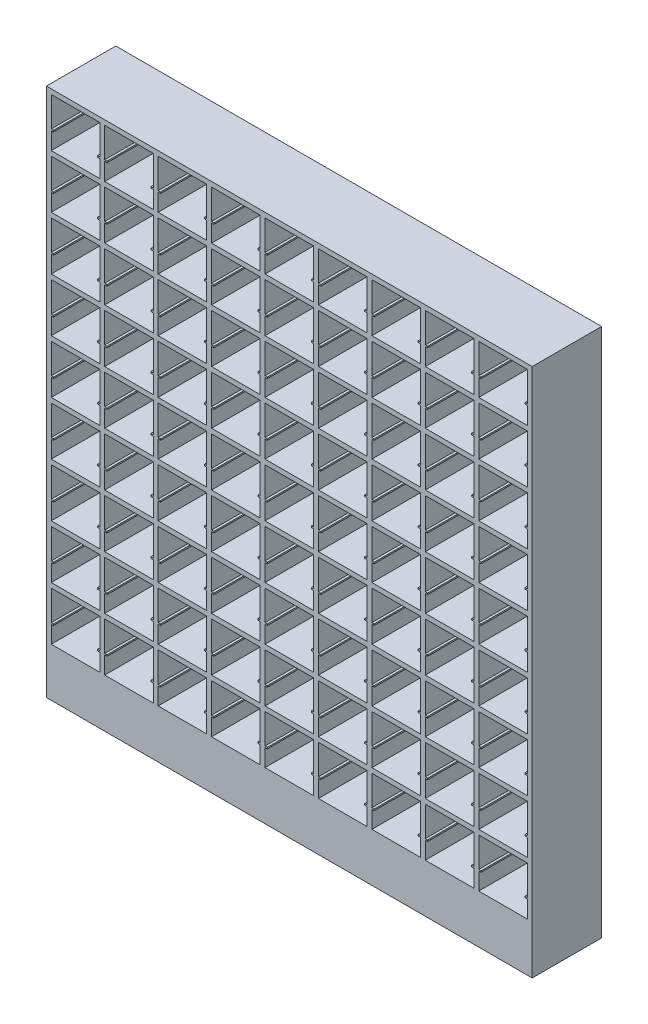
SolidWorks part; units mm, degrees
ref_plane "Alzado" through (0, 0, 0) normal (0, 0, 1) x (1, 0, 0)
ref_plane "Planta" through (0, 0, 0) normal (0, 1, 0) x (1, 0, 0)
ref_plane "Vista lateral" through (0, 0, 0) normal (1, 0, 0) x (0, 0, -1)
sketch "Croquis1" plane through (0, 0, 0) normal (0, 0, 1) x (1, 0, 0)
  line L11 (-1365, 1490) -> (-1365, 1365)
  line L330 (1750, -1750) -> (1750, 1750)
  line L331 (1750, 1750) -> (-1750, 1750)
  line L332 (-1750, -1750) -> (-1750, 1750)
  line L989 (1750, -1750) -> (-1750, 1750) construction
  line L990 (1750, 1750) -> (-1750, -1750) construction
  line L991 (-1715, 1715) -> (-1365, 1715)
  line L992 (-1715, 1715) -> (-1715, 1500)
  line L993 (-1715, 1365) -> (-1365, 1365)
  line L994 (-1365, 1715) -> (-1365, 1500)
  line L995 (-1715, 1490) -> (-1698.3333, 1490)
  line L996 (-1715, 1500) -> (-1698.3333, 1500)
  line L997 (-1698.3333, 1490) -> (-1698.3333, 1500)
  line L998 (-1365, 1490) -> (-1381.6667, 1490)
  line L1000 (-1365, 1500) -> (-1381.6667, 1500)
  line L1001 (-1381.6667, 1490) -> (-1381.6667, 1500)
  line L1002 (-1715, 1490) -> (-1715, 1365)
  line L1003 (-1330, 1715) -> (-980, 1715)
  line L1005 (-980, 1715) -> (-980, 1500)
  line L1006 (-980, 1500) -> (-996.6667, 1500)
  line L1007 (-996.6667, 1490) -> (-996.6667, 1500)
  line L1008 (-980, 1490) -> (-996.6667, 1490)
  line L1009 (-980, 1490) -> (-980, 1365)
  line L1010 (-1330, 1365) -> (-980, 1365)
  line L1011 (-1330, 1490) -> (-1330, 1365)
  line L1012 (-1330, 1490) -> (-1313.3333, 1490)
  line L1013 (-1313.3333, 1490) -> (-1313.3333, 1500)
  line L1014 (-1330, 1500) -> (-1313.3333, 1500)
  line L1015 (-1330, 1715) -> (-1330, 1500)
  line L1016 (-945, 1715) -> (-595, 1715)
  line L1017 (-595, 1715) -> (-595, 1500)
  line L1018 (-595, 1500) -> (-611.6667, 1500)
  line L1019 (-611.6667, 1490) -> (-611.6667, 1500)
  line L1020 (-595, 1490) -> (-611.6667, 1490)
  line L1021 (-595, 1490) -> (-595, 1365)
  line L1022 (-945, 1365) -> (-595, 1365)
  line L1023 (-945, 1490) -> (-945, 1365)
  line L1024 (-945, 1490) -> (-928.3333, 1490)
  line L1025 (-928.3333, 1490) -> (-928.3333, 1500)
  line L1026 (-945, 1500) -> (-928.3333, 1500)
  line L1027 (-945, 1715) -> (-945, 1500)
  line L1028 (-560, 1715) -> (-210, 1715)
  line L1029 (-210, 1715) -> (-210, 1500)
  line L1030 (-210, 1500) -> (-226.6667, 1500)
  line L1031 (-226.6667, 1490) -> (-226.6667, 1500)
  line L1032 (-210, 1490) -> (-226.6667, 1490)
  line L1033 (-210, 1490) -> (-210, 1365)
  line L1034 (-560, 1365) -> (-210, 1365)
  line L1035 (-560, 1490) -> (-560, 1365)
  line L1036 (-560, 1490) -> (-543.3333, 1490)
  line L1037 (-543.3333, 1490) -> (-543.3333, 1500)
  line L1038 (-560, 1500) -> (-543.3333, 1500)
  line L1039 (-560, 1715) -> (-560, 1500)
  line L1040 (-175, 1715) -> (175, 1715)
  line L1041 (175, 1715) -> (175, 1500)
  line L1042 (175, 1500) -> (158.3333, 1500)
  line L1043 (158.3333, 1490) -> (158.3333, 1500)
  line L1044 (175, 1490) -> (158.3333, 1490)
  line L1045 (175, 1490) -> (175, 1365)
  line L1046 (-175, 1365) -> (175, 1365)
  line L1047 (-175, 1490) -> (-175, 1365)
  line L1048 (-175, 1490) -> (-158.3333, 1490)
  line L1049 (-158.3333, 1490) -> (-158.3333, 1500)
  line L1050 (-175, 1500) -> (-158.3333, 1500)
  line L1051 (-175, 1715) -> (-175, 1500)
  line L1052 (210, 1715) -> (560, 1715)
  line L1053 (560, 1715) -> (560, 1500)
  line L1054 (560, 1500) -> (543.3333, 1500)
  line L1055 (543.3333, 1490) -> (543.3333, 1500)
  line L1056 (560, 1490) -> (543.3333, 1490)
  line L1057 (560, 1490) -> (560, 1365)
  line L1058 (210, 1365) -> (560, 1365)
  line L1059 (210, 1490) -> (210, 1365)
  line L1060 (210, 1490) -> (226.6667, 1490)
  line L1061 (226.6667, 1490) -> (226.6667, 1500)
  line L1062 (210, 1500) -> (226.6667, 1500)
  line L1063 (210, 1715) -> (210, 1500)
  line L1064 (595, 1715) -> (945, 1715)
  line L1065 (945, 1715) -> (945, 1500)
  line L1066 (945, 1500) -> (928.3333, 1500)
  line L1067 (928.3333, 1490) -> (928.3333, 1500)
  line L1068 (945, 1490) -> (928.3333, 1490)
  line L1069 (945, 1490) -> (945, 1365)
  line L1070 (595, 1365) -> (945, 1365)
  line L1071 (595, 1490) -> (595, 1365)
  line L1072 (595, 1490) -> (611.6667, 1490)
  line L1073 (611.6667, 1490) -> (611.6667, 1500)
  line L1074 (595, 1500) -> (611.6667, 1500)
  line L1075 (595, 1715) -> (595, 1500)
  line L1076 (980, 1715) -> (1330, 1715)
  line L1077 (1330, 1715) -> (1330, 1500)
  line L1078 (1330, 1500) -> (1313.3333, 1500)
  line L1079 (1313.3333, 1490) -> (1313.3333, 1500)
  line L1080 (1330, 1490) -> (1313.3333, 1490)
  line L1081 (1330, 1490) -> (1330, 1365)
  line L1082 (980, 1365) -> (1330, 1365)
  line L1083 (980, 1490) -> (980, 1365)
  line L1084 (980, 1490) -> (996.6667, 1490)
  line L1085 (996.6667, 1490) -> (996.6667, 1500)
  line L1086 (980, 1500) -> (996.6667, 1500)
  line L1087 (980, 1715) -> (980, 1500)
  line L1088 (1365, 1715) -> (1715, 1715)
  line L1089 (1715, 1715) -> (1715, 1500)
  line L1090 (1715, 1500) -> (1698.3333, 1500)
  line L1091 (1698.3333, 1490) -> (1698.3333, 1500)
  line L1092 (1715, 1490) -> (1698.3333, 1490)
  line L1093 (1715, 1490) -> (1715, 1365)
  line L1094 (1365, 1365) -> (1715, 1365)
  line L1095 (1365, 1490) -> (1365, 1365)
  line L1096 (1365, 1490) -> (1381.6667, 1490)
  line L1097 (1381.6667, 1490) -> (1381.6667, 1500)
  line L1098 (1365, 1500) -> (1381.6667, 1500)
  line L1099 (1365, 1715) -> (1365, 1500)
  line L1100 (-1330, 1330) -> (-980, 1330)
  line L1101 (-980, 1330) -> (-980, 1115)
  line L1102 (-980, 1115) -> (-996.6667, 1115)
  line L1103 (-996.6667, 1105) -> (-996.6667, 1115)
  line L1104 (-980, 1105) -> (-996.6667, 1105)
  line L1105 (-980, 1105) -> (-980, 980)
  line L1106 (-1330, 980) -> (-980, 980)
  line L1107 (-1330, 1105) -> (-1330, 980)
  line L1108 (-1330, 1105) -> (-1313.3333, 1105)
  line L1109 (-1313.3333, 1105) -> (-1313.3333, 1115)
  line L1110 (-1330, 1115) -> (-1313.3333, 1115)
  line L1111 (-1330, 1330) -> (-1330, 1115)
  line L1112 (-945, 1330) -> (-595, 1330)
  line L1113 (-595, 1330) -> (-595, 1115)
  line L1114 (-595, 1115) -> (-611.6667, 1115)
  line L1115 (-611.6667, 1105) -> (-611.6667, 1115)
  line L1116 (-595, 1105) -> (-611.6667, 1105)
  line L1117 (-595, 1105) -> (-595, 980)
  line L1118 (-945, 980) -> (-595, 980)
  line L1119 (-945, 1105) -> (-945, 980)
  line L1120 (-945, 1105) -> (-928.3333, 1105)
  line L1121 (-928.3333, 1105) -> (-928.3333, 1115)
  line L1122 (-945, 1115) -> (-928.3333, 1115)
  line L1123 (-945, 1330) -> (-945, 1115)
  line L1124 (-560, 1330) -> (-210, 1330)
  line L1125 (-210, 1330) -> (-210, 1115)
  line L1126 (-210, 1115) -> (-226.6667, 1115)
  line L1127 (-226.6667, 1105) -> (-226.6667, 1115)
  line L1128 (-210, 1105) -> (-226.6667, 1105)
  line L1129 (-210, 1105) -> (-210, 980)
  line L1130 (-560, 980) -> (-210, 980)
  line L1131 (-560, 1105) -> (-560, 980)
  line L1132 (-560, 1105) -> (-543.3333, 1105)
  line L1133 (-543.3333, 1105) -> (-543.3333, 1115)
  line L1134 (-560, 1115) -> (-543.3333, 1115)
  line L1135 (-560, 1330) -> (-560, 1115)
  line L1136 (-175, 1330) -> (175, 1330)
  line L1137 (175, 1330) -> (175, 1115)
  line L1138 (175, 1115) -> (158.3333, 1115)
  line L1139 (158.3333, 1105) -> (158.3333, 1115)
  line L1140 (175, 1105) -> (158.3333, 1105)
  line L1141 (175, 1105) -> (175, 980)
  line L1142 (-175, 980) -> (175, 980)
  line L1143 (-175, 1105) -> (-175, 980)
  line L1144 (-175, 1105) -> (-158.3333, 1105)
  line L1145 (-158.3333, 1105) -> (-158.3333, 1115)
  line L1146 (-175, 1115) -> (-158.3333, 1115)
  line L1147 (-175, 1330) -> (-175, 1115)
  line L1148 (210, 1330) -> (560, 1330)
  line L1149 (560, 1330) -> (560, 1115)
  line L1150 (560, 1115) -> (543.3333, 1115)
  line L1151 (543.3333, 1105) -> (543.3333, 1115)
  line L1152 (560, 1105) -> (543.3333, 1105)
  line L1153 (560, 1105) -> (560, 980)
  line L1154 (210, 980) -> (560, 980)
  line L1155 (210, 1105) -> (210, 980)
  line L1156 (210, 1105) -> (226.6667, 1105)
  line L1157 (226.6667, 1105) -> (226.6667, 1115)
  line L1158 (210, 1115) -> (226.6667, 1115)
  line L1159 (210, 1330) -> (210, 1115)
  line L1160 (595, 1330) -> (945, 1330)
  line L1161 (945, 1330) -> (945, 1115)
  line L1162 (945, 1115) -> (928.3333, 1115)
  line L1163 (928.3333, 1105) -> (928.3333, 1115)
  line L1164 (945, 1105) -> (928.3333, 1105)
  line L1165 (945, 1105) -> (945, 980)
  line L1166 (595, 980) -> (945, 980)
  line L1167 (595, 1105) -> (595, 980)
  line L1168 (595, 1105) -> (611.6667, 1105)
  line L1169 (611.6667, 1105) -> (611.6667, 1115)
  line L1170 (595, 1115) -> (611.6667, 1115)
  line L1171 (595, 1330) -> (595, 1115)
  line L1172 (980, 1330) -> (1330, 1330)
  line L1173 (1330, 1330) -> (1330, 1115)
  line L1174 (1330, 1115) -> (1313.3333, 1115)
  line L1175 (1313.3333, 1105) -> (1313.3333, 1115)
  line L1176 (1330, 1105) -> (1313.3333, 1105)
  line L1177 (1330, 1105) -> (1330, 980)
  line L1178 (980, 980) -> (1330, 980)
  line L1179 (980, 1105) -> (980, 980)
  line L1180 (980, 1105) -> (996.6667, 1105)
  line L1181 (996.6667, 1105) -> (996.6667, 1115)
  line L1182 (980, 1115) -> (996.6667, 1115)
  line L1183 (980, 1330) -> (980, 1115)
  line L1184 (1365, 1330) -> (1715, 1330)
  line L1185 (1715, 1330) -> (1715, 1115)
  line L1186 (1715, 1115) -> (1698.3333, 1115)
  line L1187 (1698.3333, 1105) -> (1698.3333, 1115)
  line L1188 (1715, 1105) -> (1698.3333, 1105)
  line L1189 (1715, 1105) -> (1715, 980)
  line L1190 (1365, 980) -> (1715, 980)
  line L1191 (1365, 1105) -> (1365, 980)
  line L1192 (1365, 1105) -> (1381.6667, 1105)
  line L1193 (1381.6667, 1105) -> (1381.6667, 1115)
  line L1194 (1365, 1115) -> (1381.6667, 1115)
  line L1195 (1365, 1330) -> (1365, 1115)
  line L1196 (-1330, 945) -> (-980, 945)
  line L1197 (-980, 945) -> (-980, 730)
  line L1198 (-980, 730) -> (-996.6667, 730)
  line L1199 (-996.6667, 720) -> (-996.6667, 730)
  line L1200 (-980, 720) -> (-996.6667, 720)
  line L1201 (-980, 720) -> (-980, 595)
  line L1202 (-1330, 595) -> (-980, 595)
  line L1203 (-1330, 720) -> (-1330, 595)
  line L1204 (-1330, 720) -> (-1313.3333, 720)
  line L1205 (-1313.3333, 720) -> (-1313.3333, 730)
  line L1206 (-1330, 730) -> (-1313.3333, 730)
  line L1207 (-1330, 945) -> (-1330, 730)
  line L1208 (-945, 945) -> (-595, 945)
  line L1209 (-595, 945) -> (-595, 730)
  line L1210 (-595, 730) -> (-611.6667, 730)
  line L1211 (-611.6667, 720) -> (-611.6667, 730)
  line L1212 (-595, 720) -> (-611.6667, 720)
  line L1213 (-595, 720) -> (-595, 595)
  line L1214 (-945, 595) -> (-595, 595)
  line L1215 (-945, 720) -> (-945, 595)
  line L1216 (-945, 720) -> (-928.3333, 720)
  line L1217 (-928.3333, 720) -> (-928.3333, 730)
  line L1218 (-945, 730) -> (-928.3333, 730)
  line L1219 (-945, 945) -> (-945, 730)
  line L1220 (-560, 945) -> (-210, 945)
  line L1221 (-210, 945) -> (-210, 730)
  line L1222 (-210, 730) -> (-226.6667, 730)
  line L1223 (-226.6667, 720) -> (-226.6667, 730)
  line L1224 (-210, 720) -> (-226.6667, 720)
  line L1225 (-210, 720) -> (-210, 595)
  line L1226 (-560, 595) -> (-210, 595)
  line L1227 (-560, 720) -> (-560, 595)
  line L1228 (-560, 720) -> (-543.3333, 720)
  line L1229 (-543.3333, 720) -> (-543.3333, 730)
  line L1230 (-560, 730) -> (-543.3333, 730)
  line L1231 (-560, 945) -> (-560, 730)
  line L1232 (-175, 945) -> (175, 945)
  line L1233 (175, 945) -> (175, 730)
  line L1234 (175, 730) -> (158.3333, 730)
  line L1235 (158.3333, 720) -> (158.3333, 730)
  line L1236 (175, 720) -> (158.3333, 720)
  line L1237 (175, 720) -> (175, 595)
  line L1238 (-175, 595) -> (175, 595)
  line L1239 (-175, 720) -> (-175, 595)
  line L1240 (-175, 720) -> (-158.3333, 720)
  line L1241 (-158.3333, 720) -> (-158.3333, 730)
  line L1242 (-175, 730) -> (-158.3333, 730)
  line L1244 (-175, 945) -> (-175, 730)
  line L1245 (210, 945) -> (560, 945)
  line L1246 (560, 945) -> (560, 730)
  line L1247 (560, 730) -> (543.3333, 730)
  line L1248 (543.3333, 720) -> (543.3333, 730)
  line L1249 (560, 720) -> (543.3333, 720)
  line L1250 (560, 720) -> (560, 595)
  line L1251 (210, 595) -> (560, 595)
  line L1252 (210, 720) -> (210, 595)
  line L1253 (210, 720) -> (226.6667, 720)
  line L1254 (226.6667, 720) -> (226.6667, 730)
  line L1255 (210, 730) -> (226.6667, 730)
  line L1256 (210, 945) -> (210, 730)
  line L1257 (595, 945) -> (945, 945)
  line L1258 (945, 945) -> (945, 730)
  line L1259 (945, 730) -> (928.3333, 730)
  line L1260 (928.3333, 720) -> (928.3333, 730)
  line L1261 (945, 720) -> (928.3333, 720)
  line L1262 (945, 720) -> (945, 595)
  line L1263 (595, 595) -> (945, 595)
  line L1264 (595, 720) -> (595, 595)
  line L1265 (595, 720) -> (611.6667, 720)
  line L1266 (611.6667, 720) -> (611.6667, 730)
  line L1267 (595, 730) -> (611.6667, 730)
  line L1268 (595, 945) -> (595, 730)
  line L1269 (980, 945) -> (1330, 945)
  line L1270 (1330, 945) -> (1330, 730)
  line L1271 (1330, 730) -> (1313.3333, 730)
  line L1272 (1313.3333, 720) -> (1313.3333, 730)
  line L1273 (1330, 720) -> (1313.3333, 720)
  line L1274 (1330, 720) -> (1330, 595)
  line L1275 (980, 595) -> (1330, 595)
  line L1276 (980, 720) -> (980, 595)
  line L1277 (980, 720) -> (996.6667, 720)
  line L1278 (996.6667, 720) -> (996.6667, 730)
  line L1279 (980, 730) -> (996.6667, 730)
  line L1280 (980, 945) -> (980, 730)
  line L1281 (1365, 945) -> (1715, 945)
  line L1282 (1715, 945) -> (1715, 730)
  line L1283 (1715, 730) -> (1698.3333, 730)
  line L1284 (1698.3333, 720) -> (1698.3333, 730)
  line L1285 (1715, 720) -> (1698.3333, 720)
  line L1286 (1715, 720) -> (1715, 595)
  line L1287 (1365, 595) -> (1715, 595)
  line L1288 (1365, 720) -> (1365, 595)
  line L1289 (1365, 720) -> (1381.6667, 720)
  line L1290 (1381.6667, 720) -> (1381.6667, 730)
  line L1291 (1365, 730) -> (1381.6667, 730)
  line L1292 (1365, 945) -> (1365, 730)
  line L1293 (-1330, 560) -> (-980, 560)
  line L1294 (-980, 560) -> (-980, 345)
  line L1295 (-980, 345) -> (-996.6667, 345)
  line L1296 (-996.6667, 335) -> (-996.6667, 345)
  line L1297 (-980, 335) -> (-996.6667, 335)
  line L1298 (-980, 335) -> (-980, 210)
  line L1299 (-1330, 210) -> (-980, 210)
  line L1300 (-1330, 335) -> (-1330, 210)
  line L1301 (-1330, 335) -> (-1313.3333, 335)
  line L1302 (-1313.3333, 335) -> (-1313.3333, 345)
  line L1303 (-1330, 345) -> (-1313.3333, 345)
  line L1304 (-1330, 560) -> (-1330, 345)
  line L1305 (-945, 560) -> (-595, 560)
  line L1306 (-595, 560) -> (-595, 345)
  line L1307 (-595, 345) -> (-611.6667, 345)
  line L1308 (-611.6667, 335) -> (-611.6667, 345)
  line L1309 (-595, 335) -> (-611.6667, 335)
  line L1310 (-595, 335) -> (-595, 210)
  line L1311 (-945, 210) -> (-595, 210)
  line L1312 (-945, 335) -> (-945, 210)
  line L1313 (-945, 335) -> (-928.3333, 335)
  line L1314 (-928.3333, 335) -> (-928.3333, 345)
  line L1315 (-945, 345) -> (-928.3333, 345)
  line L1316 (-945, 560) -> (-945, 345)
  line L1317 (-560, 560) -> (-210, 560)
  line L1318 (-210, 560) -> (-210, 345)
  line L1319 (-210, 345) -> (-226.6667, 345)
  line L1320 (-226.6667, 335) -> (-226.6667, 345)
  line L1321 (-210, 335) -> (-226.6667, 335)
  line L1322 (-210, 335) -> (-210, 210)
  line L1323 (-560, 210) -> (-210, 210)
  line L1324 (-560, 335) -> (-560, 210)
  line L1325 (-560, 335) -> (-543.3333, 335)
  line L1326 (-543.3333, 335) -> (-543.3333, 345)
  line L1327 (-560, 345) -> (-543.3333, 345)
  line L1328 (-560, 560) -> (-560, 345)
  line L1329 (-175, 560) -> (175, 560)
  line L1330 (175, 560) -> (175, 345)
  line L1331 (175, 345) -> (158.3333, 345)
  line L1332 (158.3333, 335) -> (158.3333, 345)
  line L1333 (175, 335) -> (158.3333, 335)
  line L1334 (175, 335) -> (175, 210)
  line L1335 (-175, 210) -> (175, 210)
  line L1336 (-175, 335) -> (-175, 210)
  line L1337 (-175, 335) -> (-158.3333, 335)
  line L1338 (-158.3333, 335) -> (-158.3333, 345)
  line L1339 (-175, 345) -> (-158.3333, 345)
  line L1340 (-175, 560) -> (-175, 345)
  line L1341 (210, 560) -> (560, 560)
  line L1342 (560, 560) -> (560, 345)
  line L1343 (560, 345) -> (543.3333, 345)
  line L1344 (543.3333, 335) -> (543.3333, 345)
  line L1345 (560, 335) -> (543.3333, 335)
  line L1346 (560, 335) -> (560, 210)
  line L1347 (210, 210) -> (560, 210)
  line L1348 (210, 335) -> (210, 210)
  line L1349 (210, 335) -> (226.6667, 335)
  line L1350 (226.6667, 335) -> (226.6667, 345)
  line L1351 (210, 345) -> (226.6667, 345)
  line L1352 (210, 560) -> (210, 345)
  line L1353 (595, 560) -> (945, 560)
  line L1354 (945, 560) -> (945, 345)
  line L1355 (945, 345) -> (928.3333, 345)
  line L1356 (928.3333, 335) -> (928.3333, 345)
  line L1357 (945, 335) -> (928.3333, 335)
  line L1358 (945, 335) -> (945, 210)
  line L1359 (595, 210) -> (945, 210)
  line L1360 (595, 335) -> (595, 210)
  line L1361 (595, 335) -> (611.6667, 335)
  line L1362 (611.6667, 335) -> (611.6667, 345)
  line L1363 (595, 345) -> (611.6667, 345)
  line L1364 (595, 560) -> (595, 345)
  line L1365 (980, 560) -> (1330, 560)
  line L1366 (1330, 560) -> (1330, 345)
  line L1367 (1330, 345) -> (1313.3333, 345)
  line L1368 (1313.3333, 335) -> (1313.3333, 345)
  line L1369 (1330, 335) -> (1313.3333, 335)
  line L1370 (1330, 335) -> (1330, 210)
  line L1371 (980, 210) -> (1330, 210)
  line L1372 (980, 335) -> (980, 210)
  line L1373 (980, 335) -> (996.6667, 335)
  line L1374 (996.6667, 335) -> (996.6667, 345)
  line L1375 (980, 345) -> (996.6667, 345)
  line L1376 (980, 560) -> (980, 345)
  line L1377 (1365, 560) -> (1715, 560)
  line L1378 (1715, 560) -> (1715, 345)
  line L1379 (1715, 345) -> (1698.3333, 345)
  line L1380 (1698.3333, 335) -> (1698.3333, 345)
  line L1381 (1715, 335) -> (1698.3333, 335)
  line L1382 (1715, 335) -> (1715, 210)
  line L1383 (1365, 210) -> (1715, 210)
  line L1384 (1365, 335) -> (1365, 210)
  line L1385 (1365, 335) -> (1381.6667, 335)
  line L1386 (1381.6667, 335) -> (1381.6667, 345)
  line L1387 (1365, 345) -> (1381.6667, 345)
  line L1388 (1365, 560) -> (1365, 345)
  line L1389 (-1330, 175) -> (-980, 175)
  line L1390 (-980, 175) -> (-980, -40)
  line L1391 (-980, -40) -> (-996.6667, -40)
  line L1392 (-996.6667, -50) -> (-996.6667, -40)
  line L1393 (-980, -50) -> (-996.6667, -50)
  line L1394 (-980, -50) -> (-980, -175)
  line L1395 (-1330, -175) -> (-980, -175)
  line L1396 (-1330, -50) -> (-1330, -175)
  line L1397 (-1330, -50) -> (-1313.3333, -50)
  line L1398 (-1313.3333, -50) -> (-1313.3333, -40)
  line L1399 (-1330, -40) -> (-1313.3333, -40)
  line L1400 (-1330, 175) -> (-1330, -40)
  line L1401 (-945, 175) -> (-595, 175)
  line L1402 (-595, 175) -> (-595, -40)
  line L1403 (-595, -40) -> (-611.6667, -40)
  line L1404 (-611.6667, -50) -> (-611.6667, -40)
  line L1405 (-595, -50) -> (-611.6667, -50)
  line L1406 (-595, -50) -> (-595, -175)
  line L1407 (-945, -175) -> (-595, -175)
  line L1408 (-945, -50) -> (-945, -175)
  line L1409 (-945, -50) -> (-928.3333, -50)
  line L1410 (-928.3333, -50) -> (-928.3333, -40)
  line L1411 (-945, -40) -> (-928.3333, -40)
  line L1412 (-945, 175) -> (-945, -40)
  line L1413 (-560, 175) -> (-210, 175)
  line L1414 (-210, 175) -> (-210, -40)
  line L1415 (-210, -40) -> (-226.6667, -40)
  line L1416 (-226.6667, -50) -> (-226.6667, -40)
  line L1417 (-210, -50) -> (-226.6667, -50)
  line L1418 (-210, -50) -> (-210, -175)
  line L1419 (-560, -175) -> (-210, -175)
  line L1420 (-560, -50) -> (-560, -175)
  line L1421 (-560, -50) -> (-543.3333, -50)
  line L1422 (-543.3333, -50) -> (-543.3333, -40)
  line L1423 (-560, -40) -> (-543.3333, -40)
  line L1424 (-560, 175) -> (-560, -40)
  line L1425 (-175, 175) -> (175, 175)
  line L1426 (175, 175) -> (175, -40)
  line L1427 (175, -40) -> (158.3333, -40)
  line L1428 (158.3333, -50) -> (158.3333, -40)
  line L1429 (175, -50) -> (158.3333, -50)
  line L1430 (175, -50) -> (175, -175)
  line L1431 (-175, -175) -> (175, -175)
  line L1432 (-175, -50) -> (-175, -175)
  line L1433 (-175, -50) -> (-158.3333, -50)
  line L1434 (-158.3333, -50) -> (-158.3333, -40)
  line L1435 (-175, -40) -> (-158.3333, -40)
  line L1436 (-175, 175) -> (-175, -40)
  line L1437 (210, 175) -> (560, 175)
  line L1438 (560, 175) -> (560, -40)
  line L1439 (560, -40) -> (543.3333, -40)
  line L1440 (543.3333, -50) -> (543.3333, -40)
  line L1441 (560, -50) -> (543.3333, -50)
  line L1442 (560, -50) -> (560, -175)
  line L1443 (210, -175) -> (560, -175)
  line L1444 (210, -50) -> (210, -175)
  line L1445 (210, -50) -> (226.6667, -50)
  line L1446 (226.6667, -50) -> (226.6667, -40)
  line L1447 (210, -40) -> (226.6667, -40)
  line L1448 (210, 175) -> (210, -40)
  line L1449 (595, 175) -> (945, 175)
  line L1450 (945, 175) -> (945, -40)
  line L1451 (945, -40) -> (928.3333, -40)
  line L1452 (928.3333, -50) -> (928.3333, -40)
  line L1453 (945, -50) -> (928.3333, -50)
  line L1454 (945, -50) -> (945, -175)
  line L1455 (595, -175) -> (945, -175)
  line L1456 (595, -50) -> (595, -175)
  line L1457 (595, -50) -> (611.6667, -50)
  line L1458 (611.6667, -50) -> (611.6667, -40)
  line L1459 (595, -40) -> (611.6667, -40)
  line L1460 (595, 175) -> (595, -40)
  line L1461 (980, 175) -> (1330, 175)
  line L1462 (1330, 175) -> (1330, -40)
  line L1463 (1330, -40) -> (1313.3333, -40)
  line L1464 (1313.3333, -50) -> (1313.3333, -40)
  line L1465 (1330, -50) -> (1313.3333, -50)
  line L1466 (1330, -50) -> (1330, -175)
  line L1467 (980, -175) -> (1330, -175)
  line L1468 (980, -50) -> (980, -175)
  line L1469 (980, -50) -> (996.6667, -50)
  line L1470 (996.6667, -50) -> (996.6667, -40)
  line L1471 (980, -40) -> (996.6667, -40)
  line L1472 (980, 175) -> (980, -40)
  line L1473 (1365, 175) -> (1715, 175)
  line L1474 (1715, 175) -> (1715, -40)
  line L1475 (1715, -40) -> (1698.3333, -40)
  line L1476 (1698.3333, -50) -> (1698.3333, -40)
  line L1477 (1715, -50) -> (1698.3333, -50)
  line L1478 (1715, -50) -> (1715, -175)
  line L1479 (1365, -175) -> (1715, -175)
  line L1480 (1365, -50) -> (1365, -175)
  line L1481 (1365, -50) -> (1381.6667, -50)
  line L1482 (1381.6667, -50) -> (1381.6667, -40)
  line L1483 (1365, -40) -> (1381.6667, -40)
  line L1484 (1365, 175) -> (1365, -40)
  line L1485 (-1330, -210) -> (-980, -210)
  line L1486 (-980, -210) -> (-980, -425)
  line L1487 (-980, -425) -> (-996.6667, -425)
  line L1488 (-996.6667, -435) -> (-996.6667, -425)
  line L1489 (-980, -435) -> (-996.6667, -435)
  line L1490 (-980, -435) -> (-980, -560)
  line L1491 (-1330, -560) -> (-980, -560)
  line L1492 (-1330, -435) -> (-1330, -560)
  line L1493 (-1330, -435) -> (-1313.3333, -435)
  line L1494 (-1313.3333, -435) -> (-1313.3333, -425)
  line L1495 (-1330, -425) -> (-1313.3333, -425)
  line L1496 (-1330, -210) -> (-1330, -425)
  line L1497 (-945, -210) -> (-595, -210)
  line L1498 (-595, -210) -> (-595, -425)
  line L1499 (-595, -425) -> (-611.6667, -425)
  line L1500 (-611.6667, -435) -> (-611.6667, -425)
  line L1501 (-595, -435) -> (-611.6667, -435)
  line L1502 (-595, -435) -> (-595, -560)
  line L1503 (-945, -560) -> (-595, -560)
  line L1504 (-945, -435) -> (-945, -560)
  line L1505 (-945, -435) -> (-928.3333, -435)
  line L1506 (-928.3333, -435) -> (-928.3333, -425)
  line L1507 (-945, -425) -> (-928.3333, -425)
  line L1508 (-945, -210) -> (-945, -425)
  line L1509 (-560, -210) -> (-210, -210)
  line L1510 (-210, -210) -> (-210, -425)
  line L1511 (-210, -425) -> (-226.6667, -425)
  line L1512 (-226.6667, -435) -> (-226.6667, -425)
  line L1513 (-210, -435) -> (-226.6667, -435)
  line L1514 (-210, -435) -> (-210, -560)
  line L1515 (-560, -560) -> (-210, -560)
  line L1516 (-560, -435) -> (-560, -560)
  line L1517 (-560, -435) -> (-543.3333, -435)
  line L1518 (-543.3333, -435) -> (-543.3333, -425)
  line L1519 (-560, -425) -> (-543.3333, -425)
  line L1520 (-560, -210) -> (-560, -425)
  line L1521 (-175, -210) -> (175, -210)
  line L1522 (175, -210) -> (175, -425)
  line L1523 (175, -425) -> (158.3333, -425)
  line L1524 (158.3333, -435) -> (158.3333, -425)
  line L1525 (175, -435) -> (158.3333, -435)
  line L1526 (175, -435) -> (175, -560)
  line L1527 (-175, -560) -> (175, -560)
  line L1528 (-175, -435) -> (-175, -560)
  line L1529 (-175, -435) -> (-158.3333, -435)
  line L1530 (-158.3333, -435) -> (-158.3333, -425)
  line L1531 (-175, -425) -> (-158.3333, -425)
  line L1532 (-175, -210) -> (-175, -425)
  line L1533 (210, -210) -> (560, -210)
  line L1534 (560, -210) -> (560, -425)
  line L1535 (560, -425) -> (543.3333, -425)
  line L1536 (543.3333, -435) -> (543.3333, -425)
  line L1537 (560, -435) -> (543.3333, -435)
  line L1538 (560, -435) -> (560, -560)
  line L1539 (210, -560) -> (560, -560)
  line L1540 (210, -435) -> (210, -560)
  line L1541 (210, -435) -> (226.6667, -435)
  line L1542 (226.6667, -435) -> (226.6667, -425)
  line L1543 (210, -425) -> (226.6667, -425)
  line L1544 (210, -210) -> (210, -425)
  line L1545 (595, -210) -> (945, -210)
  line L1546 (945, -210) -> (945, -425)
  line L1547 (945, -425) -> (928.3333, -425)
  line L1548 (928.3333, -435) -> (928.3333, -425)
  line L1549 (945, -435) -> (928.3333, -435)
  line L1550 (945, -435) -> (945, -560)
  line L1551 (595, -560) -> (945, -560)
  line L1552 (595, -435) -> (595, -560)
  line L1553 (595, -435) -> (611.6667, -435)
  line L1554 (611.6667, -435) -> (611.6667, -425)
  line L1555 (595, -425) -> (611.6667, -425)
  line L1556 (595, -210) -> (595, -425)
  line L1557 (980, -210) -> (1330, -210)
  line L1558 (1330, -210) -> (1330, -425)
  line L1559 (1330, -425) -> (1313.3333, -425)
  line L1560 (1313.3333, -435) -> (1313.3333, -425)
  line L1561 (1330, -435) -> (1313.3333, -435)
  line L1562 (1330, -435) -> (1330, -560)
  line L1563 (980, -560) -> (1330, -560)
  line L1564 (980, -435) -> (980, -560)
  line L1565 (980, -435) -> (996.6667, -435)
  line L1566 (996.6667, -435) -> (996.6667, -425)
  line L1567 (980, -425) -> (996.6667, -425)
  line L1568 (980, -210) -> (980, -425)
  line L1569 (1365, -210) -> (1715, -210)
  line L1570 (1715, -210) -> (1715, -425)
  line L1571 (1715, -425) -> (1698.3333, -425)
  line L1572 (1698.3333, -435) -> (1698.3333, -425)
  line L1573 (1715, -435) -> (1698.3333, -435)
  line L1574 (1715, -435) -> (1715, -560)
  line L1575 (1365, -560) -> (1715, -560)
  line L1576 (1365, -435) -> (1365, -560)
  line L1577 (1365, -435) -> (1381.6667, -435)
  line L1578 (1381.6667, -435) -> (1381.6667, -425)
  line L1579 (1365, -425) -> (1381.6667, -425)
  line L1580 (1365, -210) -> (1365, -425)
  line L1581 (-1330, -595) -> (-980, -595)
  line L1582 (-980, -595) -> (-980, -810)
  line L1583 (-980, -810) -> (-996.6667, -810)
  line L1584 (-996.6667, -820) -> (-996.6667, -810)
  line L1585 (-980, -820) -> (-996.6667, -820)
  line L1586 (-980, -820) -> (-980, -945)
  line L1587 (-1330, -945) -> (-980, -945)
  line L1588 (-1330, -820) -> (-1330, -945)
  line L1589 (-1330, -820) -> (-1313.3333, -820)
  line L1590 (-1313.3333, -820) -> (-1313.3333, -810)
  line L1591 (-1330, -810) -> (-1313.3333, -810)
  line L1592 (-1330, -595) -> (-1330, -810)
  line L1593 (-945, -595) -> (-595, -595)
  line L1594 (-595, -595) -> (-595, -810)
  line L1595 (-595, -810) -> (-611.6667, -810)
  line L1596 (-611.6667, -820) -> (-611.6667, -810)
  line L1597 (-595, -820) -> (-611.6667, -820)
  line L1598 (-595, -820) -> (-595, -945)
  line L1599 (-945, -945) -> (-595, -945)
  line L1600 (-945, -820) -> (-945, -945)
  line L1601 (-945, -820) -> (-928.3333, -820)
  line L1602 (-928.3333, -820) -> (-928.3333, -810)
  line L1603 (-945, -810) -> (-928.3333, -810)
  line L1604 (-945, -595) -> (-945, -810)
  line L1605 (-560, -595) -> (-210, -595)
  line L1606 (-210, -595) -> (-210, -810)
  line L1607 (-210, -810) -> (-226.6667, -810)
  line L1608 (-226.6667, -820) -> (-226.6667, -810)
  line L1609 (-210, -820) -> (-226.6667, -820)
  line L1610 (-210, -820) -> (-210, -945)
  line L1611 (-560, -945) -> (-210, -945)
  line L1612 (-560, -820) -> (-560, -945)
  line L1613 (-560, -820) -> (-543.3333, -820)
  line L1614 (-543.3333, -820) -> (-543.3333, -810)
  line L1615 (-560, -810) -> (-543.3333, -810)
  line L1616 (-560, -595) -> (-560, -810)
  line L1617 (-175, -595) -> (175, -595)
  line L1618 (175, -595) -> (175, -810)
  line L1619 (175, -810) -> (158.3333, -810)
  line L1620 (158.3333, -820) -> (158.3333, -810)
  line L1621 (175, -820) -> (158.3333, -820)
  line L1622 (175, -820) -> (175, -945)
  line L1623 (-175, -945) -> (175, -945)
  line L1624 (-175, -820) -> (-175, -945)
  line L1625 (-175, -820) -> (-158.3333, -820)
  line L1626 (-158.3333, -820) -> (-158.3333, -810)
  line L1627 (-175, -810) -> (-158.3333, -810)
  line L1628 (-175, -595) -> (-175, -810)
  line L1629 (210, -595) -> (560, -595)
  line L1630 (560, -595) -> (560, -810)
  line L1631 (560, -810) -> (543.3333, -810)
  line L1632 (543.3333, -820) -> (543.3333, -810)
  line L1633 (560, -820) -> (543.3333, -820)
  line L1634 (560, -820) -> (560, -945)
  line L1635 (210, -945) -> (560, -945)
  line L1636 (210, -820) -> (210, -945)
  line L1637 (210, -820) -> (226.6667, -820)
  line L1638 (226.6667, -820) -> (226.6667, -810)
  line L1639 (210, -810) -> (226.6667, -810)
  line L1640 (210, -595) -> (210, -810)
  line L1641 (595, -595) -> (945, -595)
  line L1642 (945, -595) -> (945, -810)
  line L1643 (945, -810) -> (928.3333, -810)
  line L1644 (928.3333, -820) -> (928.3333, -810)
  line L1645 (945, -820) -> (928.3333, -820)
  line L1646 (945, -820) -> (945, -945)
  line L1647 (595, -945) -> (945, -945)
  line L1648 (595, -820) -> (595, -945)
  line L1649 (595, -820) -> (611.6667, -820)
  line L1650 (611.6667, -820) -> (611.6667, -810)
  line L1651 (595, -810) -> (611.6667, -810)
  line L1652 (595, -595) -> (595, -810)
  line L1653 (980, -595) -> (1330, -595)
  line L1654 (1330, -595) -> (1330, -810)
  line L1655 (1330, -810) -> (1313.3333, -810)
  line L1656 (1313.3333, -820) -> (1313.3333, -810)
  line L1657 (1330, -820) -> (1313.3333, -820)
  line L1658 (1330, -820) -> (1330, -945)
  line L1659 (980, -945) -> (1330, -945)
  line L1660 (980, -820) -> (980, -945)
  line L1661 (980, -820) -> (996.6667, -820)
  line L1662 (996.6667, -820) -> (996.6667, -810)
  line L1663 (980, -810) -> (996.6667, -810)
  line L1664 (980, -595) -> (980, -810)
  line L1665 (1365, -595) -> (1715, -595)
  line L1666 (1715, -595) -> (1715, -810)
  line L1667 (1715, -810) -> (1698.3333, -810)
  line L1668 (1698.3333, -820) -> (1698.3333, -810)
  line L1669 (1715, -820) -> (1698.3333, -820)
  line L1670 (1715, -820) -> (1715, -945)
  line L1671 (1365, -945) -> (1715, -945)
  line L1672 (1365, -820) -> (1365, -945)
  line L1673 (1365, -820) -> (1381.6667, -820)
  line L1674 (1381.6667, -820) -> (1381.6667, -810)
  line L1675 (1365, -810) -> (1381.6667, -810)
  line L1676 (1365, -595) -> (1365, -810)
  line L1677 (-1330, -980) -> (-980, -980)
  line L1678 (-980, -980) -> (-980, -1195)
  line L1679 (-980, -1195) -> (-996.6667, -1195)
  line L1680 (-996.6667, -1205) -> (-996.6667, -1195)
  line L1681 (-980, -1205) -> (-996.6667, -1205)
  line L1682 (-980, -1205) -> (-980, -1330)
  line L1683 (-1330, -1330) -> (-980, -1330)
  line L1684 (-1330, -1205) -> (-1330, -1330)
  line L1685 (-1330, -1205) -> (-1313.3333, -1205)
  line L1686 (-1313.3333, -1205) -> (-1313.3333, -1195)
  line L1687 (-1330, -1195) -> (-1313.3333, -1195)
  line L1688 (-1330, -980) -> (-1330, -1195)
  line L1689 (-945, -980) -> (-595, -980)
  line L1690 (-595, -980) -> (-595, -1195)
  line L1691 (-595, -1195) -> (-611.6667, -1195)
  line L1692 (-611.6667, -1205) -> (-611.6667, -1195)
  line L1693 (-595, -1205) -> (-611.6667, -1205)
  line L1694 (-595, -1205) -> (-595, -1330)
  line L1695 (-945, -1330) -> (-595, -1330)
  line L1696 (-945, -1205) -> (-945, -1330)
  line L1697 (-945, -1205) -> (-928.3333, -1205)
  line L1698 (-928.3333, -1205) -> (-928.3333, -1195)
  line L1699 (-945, -1195) -> (-928.3333, -1195)
  line L1700 (-945, -980) -> (-945, -1195)
  line L1701 (-560, -980) -> (-210, -980)
  line L1702 (-210, -980) -> (-210, -1195)
  line L1703 (-210, -1195) -> (-226.6667, -1195)
  line L1704 (-226.6667, -1205) -> (-226.6667, -1195)
  line L1705 (-210, -1205) -> (-226.6667, -1205)
  line L1706 (-210, -1205) -> (-210, -1330)
  line L1707 (-560, -1330) -> (-210, -1330)
  line L1708 (-560, -1205) -> (-560, -1330)
  line L1709 (-560, -1205) -> (-543.3333, -1205)
  line L1710 (-543.3333, -1205) -> (-543.3333, -1195)
  line L1711 (-560, -1195) -> (-543.3333, -1195)
  line L1712 (-560, -980) -> (-560, -1195)
  line L1713 (-175, -980) -> (175, -980)
  line L1714 (175, -980) -> (175, -1195)
  line L1715 (175, -1195) -> (158.3333, -1195)
  line L1716 (158.3333, -1205) -> (158.3333, -1195)
  line L1717 (175, -1205) -> (158.3333, -1205)
  line L1718 (175, -1205) -> (175, -1330)
  line L1719 (-175, -1330) -> (175, -1330)
  line L1720 (-175, -1205) -> (-175, -1330)
  line L1721 (-175, -1205) -> (-158.3333, -1205)
  line L1722 (-158.3333, -1205) -> (-158.3333, -1195)
  line L1723 (-175, -1195) -> (-158.3333, -1195)
  line L1724 (-175, -980) -> (-175, -1195)
  line L1725 (210, -980) -> (560, -980)
  line L1726 (560, -980) -> (560, -1195)
  line L1727 (560, -1195) -> (543.3333, -1195)
  line L1728 (543.3333, -1205) -> (543.3333, -1195)
  line L1729 (560, -1205) -> (543.3333, -1205)
  line L1730 (560, -1205) -> (560, -1330)
  line L1731 (210, -1330) -> (560, -1330)
  line L1732 (210, -1205) -> (210, -1330)
  line L1733 (210, -1205) -> (226.6667, -1205)
  line L1734 (226.6667, -1205) -> (226.6667, -1195)
  line L1735 (210, -1195) -> (226.6667, -1195)
  line L1736 (210, -980) -> (210, -1195)
  line L1737 (595, -980) -> (945, -980)
  line L1738 (945, -980) -> (945, -1195)
  line L1739 (945, -1195) -> (928.3333, -1195)
  line L1740 (928.3333, -1205) -> (928.3333, -1195)
  line L1741 (945, -1205) -> (928.3333, -1205)
  line L1742 (945, -1205) -> (945, -1330)
  line L1743 (595, -1330) -> (945, -1330)
  line L1744 (595, -1205) -> (595, -1330)
  line L1745 (595, -1205) -> (611.6667, -1205)
  line L1746 (611.6667, -1205) -> (611.6667, -1195)
  line L1747 (595, -1195) -> (611.6667, -1195)
  line L1748 (595, -980) -> (595, -1195)
  line L1749 (980, -980) -> (1330, -980)
  line L1750 (1330, -980) -> (1330, -1195)
  line L1751 (1330, -1195) -> (1313.3333, -1195)
  line L1752 (1313.3333, -1205) -> (1313.3333, -1195)
  line L1753 (1330, -1205) -> (1313.3333, -1205)
  line L1754 (1330, -1205) -> (1330, -1330)
  line L1755 (980, -1330) -> (1330, -1330)
  line L1756 (980, -1205) -> (980, -1330)
  line L1757 (980, -1205) -> (996.6667, -1205)
  line L1758 (996.6667, -1205) -> (996.6667, -1195)
  line L1759 (980, -1195) -> (996.6667, -1195)
  line L1760 (980, -980) -> (980, -1195)
  line L1761 (1365, -980) -> (1715, -980)
  line L1762 (1715, -980) -> (1715, -1195)
  line L1763 (1715, -1195) -> (1698.3333, -1195)
  line L1764 (1698.3333, -1205) -> (1698.3333, -1195)
  line L1765 (1715, -1205) -> (1698.3333, -1205)
  line L1766 (1715, -1205) -> (1715, -1330)
  line L1767 (1365, -1330) -> (1715, -1330)
  line L1768 (1365, -1205) -> (1365, -1330)
  line L1769 (1365, -1205) -> (1381.6667, -1205)
  line L1770 (1381.6667, -1205) -> (1381.6667, -1195)
  line L1771 (1365, -1195) -> (1381.6667, -1195)
  line L1772 (1365, -980) -> (1365, -1195)
  line L1773 (-1330, -1365) -> (-980, -1365)
  line L1774 (-980, -1365) -> (-980, -1580)
  line L1775 (-980, -1580) -> (-996.6667, -1580)
  line L1776 (-996.6667, -1590) -> (-996.6667, -1580)
  line L1777 (-980, -1590) -> (-996.6667, -1590)
  line L1778 (-980, -1590) -> (-980, -1715)
  line L1779 (-1330, -1715) -> (-980, -1715)
  line L1780 (-1330, -1590) -> (-1330, -1715)
  line L1781 (-1330, -1590) -> (-1313.3333, -1590)
  line L1782 (-1313.3333, -1590) -> (-1313.3333, -1580)
  line L1783 (-1330, -1580) -> (-1313.3333, -1580)
  line L1784 (-1330, -1365) -> (-1330, -1580)
  line L1785 (-945, -1365) -> (-595, -1365)
  line L1786 (-595, -1365) -> (-595, -1580)
  line L1787 (-595, -1580) -> (-611.6667, -1580)
  line L1788 (-611.6667, -1590) -> (-611.6667, -1580)
  line L1789 (-595, -1590) -> (-611.6667, -1590)
  line L1790 (-595, -1590) -> (-595, -1715)
  line L1791 (-945, -1715) -> (-595, -1715)
  line L1792 (-945, -1590) -> (-945, -1715)
  line L1793 (-945, -1590) -> (-928.3333, -1590)
  line L1794 (-928.3333, -1590) -> (-928.3333, -1580)
  line L1795 (-945, -1580) -> (-928.3333, -1580)
  line L1796 (-945, -1365) -> (-945, -1580)
  line L1797 (-560, -1365) -> (-210, -1365)
  line L1798 (-210, -1365) -> (-210, -1580)
  line L1799 (-210, -1580) -> (-226.6667, -1580)
  line L1800 (-226.6667, -1590) -> (-226.6667, -1580)
  line L1801 (-210, -1590) -> (-226.6667, -1590)
  line L1802 (-210, -1590) -> (-210, -1715)
  line L1803 (-560, -1715) -> (-210, -1715)
  line L1804 (-560, -1590) -> (-560, -1715)
  line L1805 (-560, -1590) -> (-543.3333, -1590)
  line L1806 (-543.3333, -1590) -> (-543.3333, -1580)
  line L1807 (-560, -1580) -> (-543.3333, -1580)
  line L1808 (-560, -1365) -> (-560, -1580)
  line L1809 (-175, -1365) -> (175, -1365)
  line L1810 (175, -1365) -> (175, -1580)
  line L1811 (175, -1580) -> (158.3333, -1580)
  line L1812 (158.3333, -1590) -> (158.3333, -1580)
  line L1813 (175, -1590) -> (158.3333, -1590)
  line L1814 (175, -1590) -> (175, -1715)
  line L1815 (-175, -1715) -> (175, -1715)
  line L1816 (-175, -1590) -> (-175, -1715)
  line L1817 (-175, -1590) -> (-158.3333, -1590)
  line L1818 (-158.3333, -1590) -> (-158.3333, -1580)
  line L1819 (-175, -1580) -> (-158.3333, -1580)
  line L1820 (-175, -1365) -> (-175, -1580)
  line L1821 (210, -1365) -> (560, -1365)
  line L1822 (560, -1365) -> (560, -1580)
  line L1823 (560, -1580) -> (543.3333, -1580)
  line L1824 (543.3333, -1590) -> (543.3333, -1580)
  line L1825 (560, -1590) -> (543.3333, -1590)
  line L1826 (560, -1590) -> (560, -1715)
  line L1827 (210, -1715) -> (560, -1715)
  line L1828 (210, -1590) -> (210, -1715)
  line L1829 (210, -1590) -> (226.6667, -1590)
  line L1830 (226.6667, -1590) -> (226.6667, -1580)
  line L1831 (210, -1580) -> (226.6667, -1580)
  line L1832 (210, -1365) -> (210, -1580)
  line L1833 (595, -1365) -> (945, -1365)
  line L1834 (945, -1365) -> (945, -1580)
  line L1835 (945, -1580) -> (928.3333, -1580)
  line L1836 (928.3333, -1590) -> (928.3333, -1580)
  line L1837 (945, -1590) -> (928.3333, -1590)
  line L1838 (945, -1590) -> (945, -1715)
  line L1839 (595, -1715) -> (945, -1715)
  line L1840 (595, -1590) -> (595, -1715)
  line L1841 (595, -1590) -> (611.6667, -1590)
  line L1842 (611.6667, -1590) -> (611.6667, -1580)
  line L1843 (595, -1580) -> (611.6667, -1580)
  line L1844 (595, -1365) -> (595, -1580)
  line L1845 (980, -1365) -> (1330, -1365)
  line L1846 (1330, -1365) -> (1330, -1580)
  line L1847 (1330, -1580) -> (1313.3333, -1580)
  line L1848 (1313.3333, -1590) -> (1313.3333, -1580)
  line L1849 (1330, -1590) -> (1313.3333, -1590)
  line L1850 (1330, -1590) -> (1330, -1715)
  line L1851 (980, -1715) -> (1330, -1715)
  line L1852 (980, -1590) -> (980, -1715)
  line L1853 (980, -1590) -> (996.6667, -1590)
  line L1854 (996.6667, -1590) -> (996.6667, -1580)
  line L1855 (980, -1580) -> (996.6667, -1580)
  line L1856 (980, -1365) -> (980, -1580)
  line L1857 (1365, -1365) -> (1715, -1365)
  line L1858 (1715, -1365) -> (1715, -1580)
  line L1859 (1715, -1580) -> (1698.3333, -1580)
  line L1860 (1698.3333, -1590) -> (1698.3333, -1580)
  line L1861 (1715, -1590) -> (1698.3333, -1590)
  line L1862 (1715, -1590) -> (1715, -1715)
  line L1863 (1365, -1715) -> (1715, -1715)
  line L1864 (1365, -1590) -> (1365, -1715)
  line L1865 (1365, -1590) -> (1381.6667, -1590)
  line L1866 (1381.6667, -1590) -> (1381.6667, -1580)
  line L1867 (1365, -1580) -> (1381.6667, -1580)
  line L1868 (1365, -1365) -> (1365, -1580)
  line L1869 (-1715, 1330) -> (-1365, 1330)
  line L1870 (-1365, 1330) -> (-1365, 1115)
  line L1871 (-1365, 1115) -> (-1381.6667, 1115)
  line L1872 (-1381.6667, 1105) -> (-1381.6667, 1115)
  line L1873 (-1365, 1105) -> (-1381.6667, 1105)
  line L1874 (-1365, 1105) -> (-1365, 980)
  line L1875 (-1715, 980) -> (-1365, 980)
  line L1876 (-1715, 1105) -> (-1715, 980)
  line L1877 (-1715, 1105) -> (-1698.3333, 1105)
  line L1878 (-1698.3333, 1105) -> (-1698.3333, 1115)
  line L1879 (-1715, 1115) -> (-1698.3333, 1115)
  line L1880 (-1715, 1330) -> (-1715, 1115)
  line L1881 (-1715, 945) -> (-1365, 945)
  line L1882 (-1365, 945) -> (-1365, 730)
  line L1883 (-1365, 730) -> (-1381.6667, 730)
  line L1884 (-1381.6667, 720) -> (-1381.6667, 730)
  line L1885 (-1365, 720) -> (-1381.6667, 720)
  line L1886 (-1365, 720) -> (-1365, 595)
  line L1887 (-1715, 595) -> (-1365, 595)
  line L1888 (-1715, 720) -> (-1715, 595)
  line L1889 (-1715, 720) -> (-1698.3333, 720)
  line L1890 (-1698.3333, 720) -> (-1698.3333, 730)
  line L1891 (-1715, 730) -> (-1698.3333, 730)
  line L1892 (-1715, 945) -> (-1715, 730)
  line L1893 (-1715, 560) -> (-1365, 560)
  line L1894 (-1365, 560) -> (-1365, 345)
  line L1895 (-1365, 345) -> (-1381.6667, 345)
  line L1896 (-1381.6667, 335) -> (-1381.6667, 345)
  line L1897 (-1365, 335) -> (-1381.6667, 335)
  line L1898 (-1365, 335) -> (-1365, 210)
  line L1899 (-1715, 210) -> (-1365, 210)
  line L1900 (-1715, 335) -> (-1715, 210)
  line L1901 (-1715, 335) -> (-1698.3333, 335)
  line L1902 (-1698.3333, 335) -> (-1698.3333, 345)
  line L1903 (-1715, 345) -> (-1698.3333, 345)
  line L1904 (-1715, 560) -> (-1715, 345)
  line L1905 (-1715, 175) -> (-1365, 175)
  line L1906 (-1365, 175) -> (-1365, -40)
  line L1907 (-1365, -40) -> (-1381.6667, -40)
  line L1908 (-1381.6667, -50) -> (-1381.6667, -40)
  line L1909 (-1365, -50) -> (-1381.6667, -50)
  line L1910 (-1365, -50) -> (-1365, -175)
  line L1911 (-1715, -175) -> (-1365, -175)
  line L1912 (-1715, -50) -> (-1715, -175)
  line L1913 (-1715, -50) -> (-1698.3333, -50)
  line L1914 (-1698.3333, -50) -> (-1698.3333, -40)
  line L1915 (-1715, -40) -> (-1698.3333, -40)
  line L1916 (-1715, 175) -> (-1715, -40)
  line L1917 (-1715, -210) -> (-1365, -210)
  line L1918 (-1365, -210) -> (-1365, -425)
  line L1919 (-1365, -425) -> (-1381.6667, -425)
  line L1920 (-1381.6667, -435) -> (-1381.6667, -425)
  line L1921 (-1365, -435) -> (-1381.6667, -435)
  line L1922 (-1365, -435) -> (-1365, -560)
  line L1923 (-1715, -560) -> (-1365, -560)
  line L1924 (-1715, -435) -> (-1715, -560)
  line L1925 (-1715, -435) -> (-1698.3333, -435)
  line L1926 (-1698.3333, -435) -> (-1698.3333, -425)
  line L1927 (-1715, -425) -> (-1698.3333, -425)
  line L1928 (-1715, -210) -> (-1715, -425)
  line L1929 (-1715, -595) -> (-1365, -595)
  line L1930 (-1365, -595) -> (-1365, -810)
  line L1931 (-1365, -810) -> (-1381.6667, -810)
  line L1932 (-1381.6667, -820) -> (-1381.6667, -810)
  line L1933 (-1365, -820) -> (-1381.6667, -820)
  line L1934 (-1365, -820) -> (-1365, -945)
  line L1935 (-1715, -945) -> (-1365, -945)
  line L1936 (-1715, -820) -> (-1715, -945)
  line L1937 (-1715, -820) -> (-1698.3333, -820)
  line L1938 (-1698.3333, -820) -> (-1698.3333, -810)
  line L1939 (-1715, -810) -> (-1698.3333, -810)
  line L1940 (-1715, -595) -> (-1715, -810)
  line L1941 (-1715, -980) -> (-1365, -980)
  line L1942 (-1365, -980) -> (-1365, -1195)
  line L1943 (-1365, -1195) -> (-1381.6667, -1195)
  line L1944 (-1381.6667, -1205) -> (-1381.6667, -1195)
  line L1945 (-1365, -1205) -> (-1381.6667, -1205)
  line L1946 (-1365, -1205) -> (-1365, -1330)
  line L1947 (-1715, -1330) -> (-1365, -1330)
  line L1948 (-1715, -1205) -> (-1715, -1330)
  line L1949 (-1715, -1205) -> (-1698.3333, -1205)
  line L1950 (-1698.3333, -1205) -> (-1698.3333, -1195)
  line L1951 (-1715, -1195) -> (-1698.3333, -1195)
  line L1952 (-1715, -980) -> (-1715, -1195)
  line L1953 (-1715, -1365) -> (-1365, -1365)
  line L1954 (-1365, -1365) -> (-1365, -1580)
  line L1955 (-1365, -1580) -> (-1381.6667, -1580)
  line L1956 (-1381.6667, -1590) -> (-1381.6667, -1580)
  line L1957 (-1365, -1590) -> (-1381.6667, -1590)
  line L1958 (-1365, -1590) -> (-1365, -1715)
  line L1959 (-1715, -1715) -> (-1365, -1715)
  line L1960 (-1715, -1590) -> (-1715, -1715)
  line L1961 (-1715, -1590) -> (-1698.3333, -1590)
  line L1962 (-1698.3333, -1590) -> (-1698.3333, -1580)
  line L1963 (-1715, -1580) -> (-1698.3333, -1580)
  line L1964 (-1715, -1365) -> (-1715, -1580)
  line L1965 (-1715, 1715) -> (-1330, 1715) construction
  line L1966 (-1715, 1715) -> (-1715, 1330) construction
  line L1967 (-1750, -1750) -> (-1750, -2065)
  line L1968 (-1750, -2065) -> (1750, -2065)
  line L1969 (1750, -1750) -> (1750, -2065)
  point P0 (0, 0)
  dimension "D1" = 3500
  dimension "D2" = 3500
  dimension "D3" = 350
  dimension "D4" = 350
  dimension "D5" = 10
  dimension "D6" = 16.6667
  dimension "D7" = 10
  dimension "D8" = 16.6667
  dimension "D11" = 35
  dimension "D12" = 35
  dimension "D13" = 90
  dimension "D14" = 385
  dimension "D15" = 385
  dimension "D16" = 9
  dimension "D17" = 9
  dimension "D18" = 315
  dimension "D9" = 125
  dimension "D10" = 125
extrude "Saliente-Extruir4" add sketch "Croquis1" along normal blind 500
